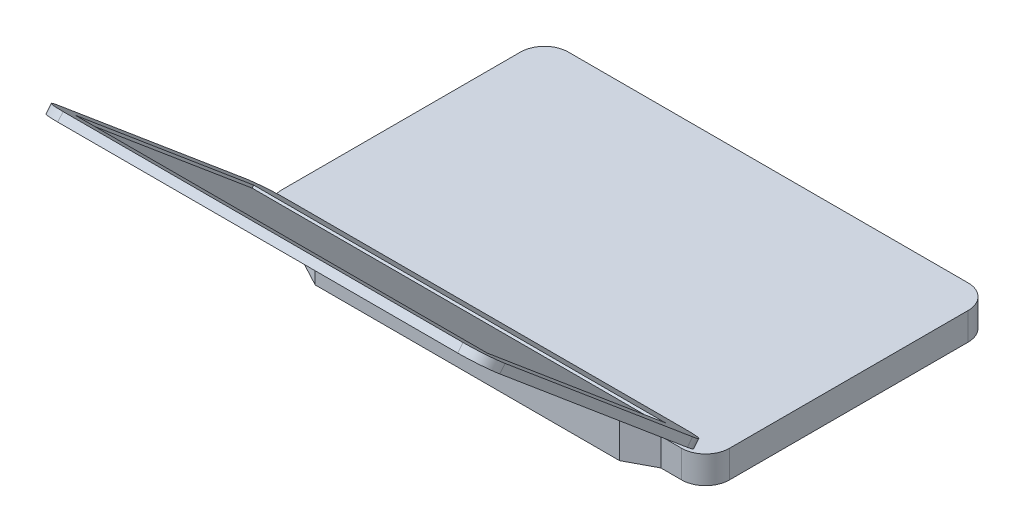
SolidWorks part; units mm, degrees
ref_plane "Front Plane" through (0, 0, 0) normal (0, 0, 1) x (1, 0, 0)
ref_plane "Top Plane" through (0, 0, 0) normal (0, 1, 0) x (1, 0, 0)
ref_plane "Right Plane" through (0, 0, 0) normal (1, 0, 0) x (0, 0, -1)
sketch "Sketch1" plane through (0, 0, 0) normal (0, 1, 0) x (1, 0, 0)
  line L1 (187.5, -120) -> (-187.5, -120)
  line L2 (187.5, -120) -> (187.5, 120)
  line L3 (187.5, 120) -> (-187.5, 120)
  line L4 (-187.5, -120) -> (-187.5, 120)
  line L5 (187.5, -120) -> (-187.5, 120) construction
  line L6 (187.5, 120) -> (-187.5, -120) construction
  point P0 (0, 0)
  dimension "D1" = 375
  dimension "D2" = 240
extrude "Boss-Extrude1" add sketch "Sketch1" along normal blind 23
sketch "Sketch3" plane through (0, 0, 0) normal (0, -1, 0) x (1, 0, 0)
  line L0 (-150, 120) -> (-127.5, 132)
  line L1 (-187.5, 120) -> (187.5, 120) construction
  line L2 (-127.5, 132) -> (127.5, 132)
  line L3 (-150, 120) -> (150, 120)
  line L4 (0, 132) -> (0, 120) construction
  line L5 (150, 120) -> (127.5, 132)
  dimension "D1" = 12
  dimension "D2" = 255
  dimension "D3" = 300
extrude "Boss-Extrude2" add sketch "Sketch3" against normal blind 34
sketch "Sketch4" plane through (-187.5, 0, 0) normal (-1, 0, 0) x (0, 0, 1)
  line L0 (120, 28.5) -> (126.5546, 34)
  line L1 (120, 34) -> (120, 23) construction
  line L2 (120, 28.5) -> (120, 34)
  line L3 (120, 34) -> (126.5546, 34)
  line L4 (-120, 23) -> (120, 23) construction
  dimension "D1" = 140
extrude "Cut-Extrude1" cut sketch "Sketch4" against normal through all
sketch "Sketch5" plane through (0, -42.364, 35.5476) normal (0, 0.766, -0.6428) x (-1, 0, 0)
  line L0 (-187.5, 106.7094) -> (-187.5, -77.1412) construction
  line L1 (187.5, 355.2448) -> (-187.5, 355.2448)
  line L2 (187.5, 355.2448) -> (187.5, 110.2448)
  line L3 (187.5, 110.2448) -> (-187.5, 110.2448)
  line L4 (-187.5, 355.2448) -> (-187.5, 110.2448)
  line L5 (187.5, 355.2448) -> (-187.5, 110.2448) construction
  line L6 (187.5, 110.2448) -> (-187.5, 355.2448) construction
  line L7 (-150, 110.2448) -> (150, 110.2448) construction
  point P0 (0, 232.7448)
  point P7 (0, 0)
  point P9 (0, 0)
  dimension "D1" = 245
extrude "Boss-Extrude3" add sketch "Sketch5" along normal blind 7
sketch "Sketch6" plane through (0, -37.0017, 31.0481) normal (0, 0.766, -0.6428) x (1, 0, 0)
  line L0 (187.5, -355.2448) -> (187.5, -110.2448) construction
  line L1 (-172.5, -140.2448) -> (172.5, -140.2448)
  line L2 (-172.5, -140.2448) -> (-172.5, -335.2448)
  line L3 (-172.5, -335.2448) -> (172.5, -335.2448)
  line L4 (172.5, -140.2448) -> (172.5, -335.2448)
  line L5 (-172.5, -140.2448) -> (172.5, -335.2448) construction
  line L6 (-172.5, -335.2448) -> (172.5, -140.2448) construction
  line L7 (-187.5, -355.2448) -> (187.5, -355.2448) construction
  line L8 (187.5, -110.2448) -> (-187.5, -110.2448) construction
  point P0 (0, -237.7448)
  point P11 (0, 0)
  dimension "D1" = 15
  dimension "D2" = 20
  dimension "D3" = 30
extrude "Cut-Extrude2" cut sketch "Sketch6" against normal blind 2
fillet "Fillet1" radius 20 8 edges at (-187.5, 11.5, -120) (187.5, 11.5, -120) (187.5, 11.5, 120) (187.5, 31.1812, 117.7502) (-187.5, 11.5, 120) (-187.5, 31.1812, 117.7502) (-187.5, 188.6641, 305.4311) (187.5, 188.6641, 305.4311)
